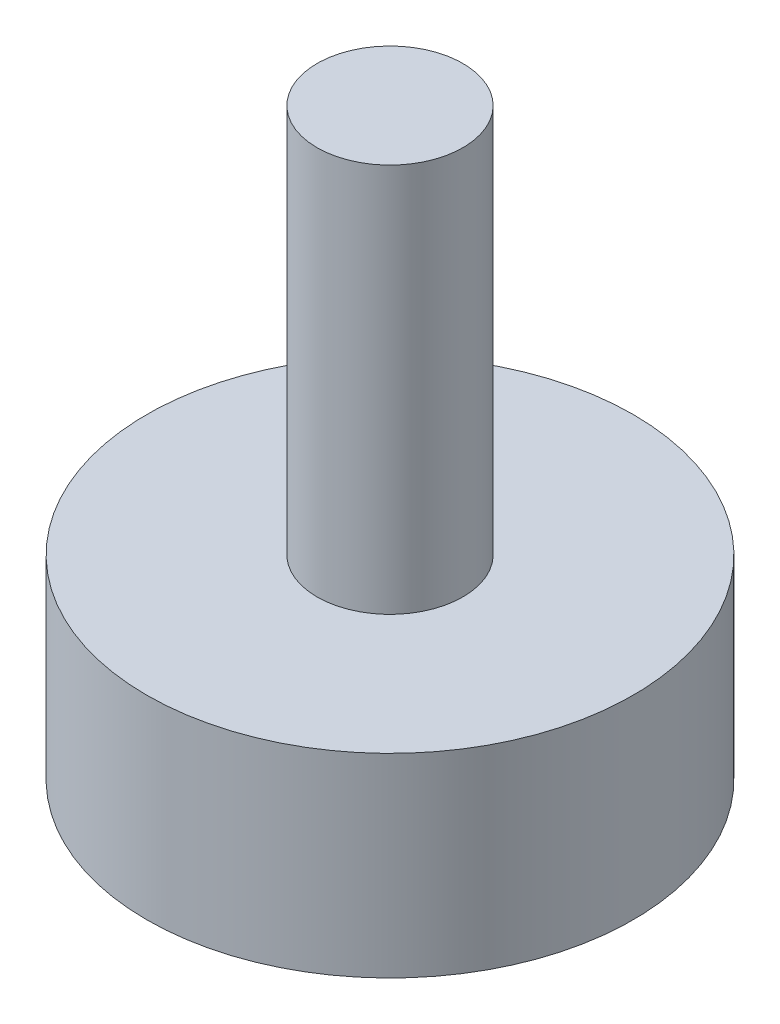
SolidWorks part; units mm, degrees
material "ZZnAl4Cu1Mg"
ref_plane "Front" through (0, 0, 0) normal (0, 0, 1) x (1, 0, 0)
ref_plane "Top" through (0, 0, 0) normal (0, 1, 0) x (1, 0, 0)
ref_plane "Right" through (0, 0, 0) normal (1, 0, 0) x (0, 0, -1)
sketch "草图1" plane through (0, 0, 0) normal (0, 1, 0) x (1, 0, 0)
  circle A0 centre (0, 0) radius 1.5
extrude "凸台-拉伸1" add sketch "草图1" along normal blind 8
sketch "草图2" plane through (0, 0, 0) normal (0, -1, 0) x (1, 0, 0)
  circle A0 centre (0, 0) radius 5
extrude "凸台-拉伸2" add sketch "草图2" along normal blind 4
